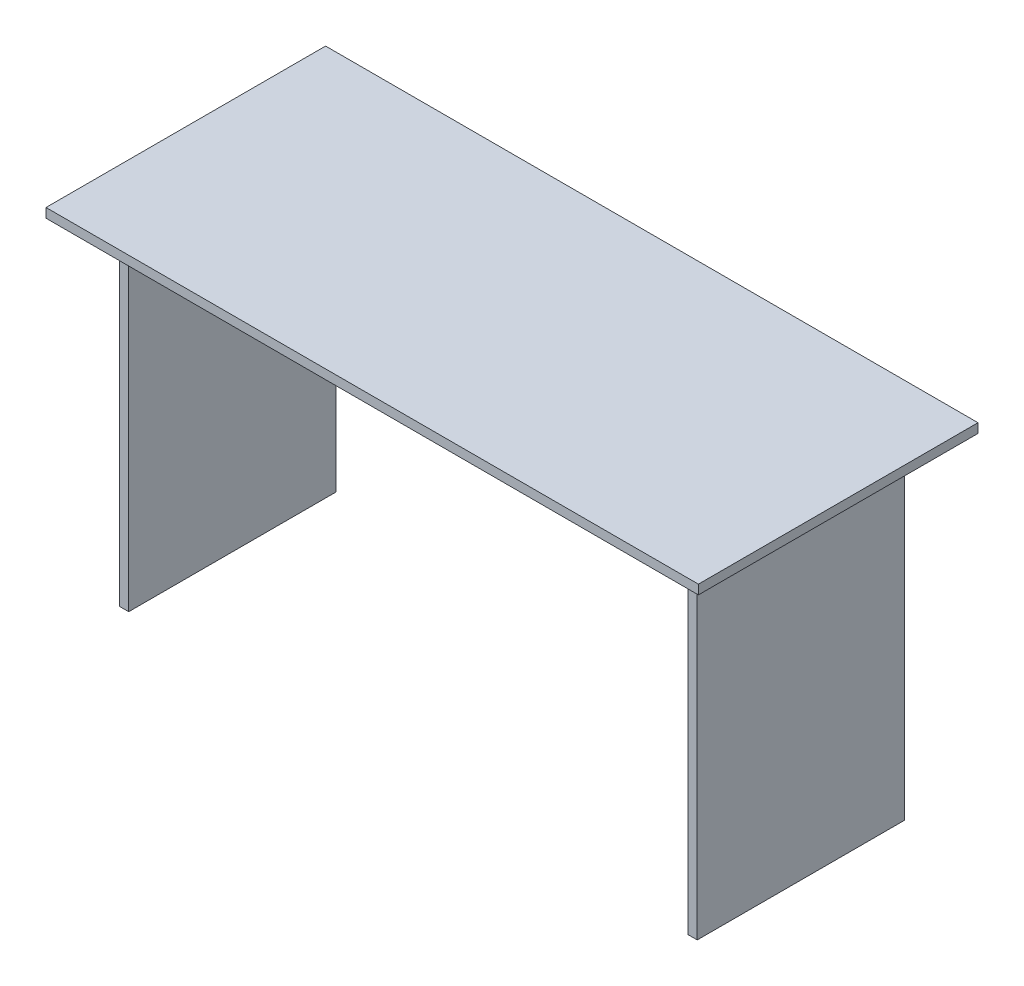
SolidWorks part; units mm, degrees
ref_plane "Front Plane" through (0, 0, 0) normal (0, 0, 1) x (1, 0, 0)
ref_plane "Top Plane" through (0, 0, 0) normal (0, 1, 0) x (1, 0, 0)
ref_plane "Right Plane" through (0, 0, 0) normal (1, 0, 0) x (0, 0, -1)
sketch "Sketch1" plane through (0, 0, 0) normal (0, 1, 0) x (1, 0, 0)
  line L1 (700, -300) -> (-700, -300)
  line L2 (700, -300) -> (700, 300)
  line L3 (700, 300) -> (-700, 300)
  line L4 (-700, -300) -> (-700, 300)
  line L5 (700, -300) -> (-700, 300) construction
  line L6 (700, 300) -> (-700, -300) construction
  point P0 (0, 0)
  dimension "D1" = 1400
  dimension "D2" = 600
extrude "Boss-Extrude1" add sketch "Sketch1" against normal blind 20
sketch "Sketch2" plane through (0, -20, 0) normal (0, -1, 0) x (1, 0, 0)
  line L0 (0, 300) -> (0, -300) construction
  line L1 (-700, 300) -> (700, 300) construction
  line L2 (700, -300) -> (-700, -300) construction
  line L3 (700, 300) -> (700, -300) construction
  line L4 (600, 222.5) -> (620, 222.5)
  line L5 (600, 222.5) -> (600, -222.5)
  line L6 (600, -222.5) -> (620, -222.5)
  line L7 (620, 222.5) -> (620, -222.5)
  line L8 (600, 222.5) -> (620, -222.5) construction
  line L9 (600, -222.5) -> (620, 222.5) construction
  line L10 (-600, -222.5) -> (-620, -222.5)
  line L11 (-620, 222.5) -> (-620, -222.5)
  line L12 (-600, 222.5) -> (-620, 222.5)
  line L13 (-600, 222.5) -> (-600, -222.5)
  point P6 (610, 0)
  point P11 (0, 0)
  dimension "D1" = 445
  dimension "D2" = 20
  dimension "D3" = 80
extrude "Boss-Extrude2" add sketch "Sketch2" along normal blind 720
sketch "Sketch3" plane through (0, -20, 0) normal (0, -1, 0) x (1, 0, 0)
  line L0 (-600, -222.5) -> (-600, 222.5) construction
  line L1 (600, -197.5) -> (-600, -197.5)
  line L2 (600, -197.5) -> (600, -177.5)
  line L3 (600, -177.5) -> (-600, -177.5)
  line L4 (-600, -197.5) -> (-600, -177.5)
  line L5 (600, -197.5) -> (-600, -177.5) construction
  line L6 (600, -177.5) -> (-600, -197.5) construction
  line L7 (600, -222.5) -> (620, -222.5) construction
  point P0 (0, -187.5)
  point P9 (0, 0)
  dimension "D1" = 20
  dimension "D2" = 25
extrude "Boss-Extrude3" add sketch "Sketch3" along normal blind 450
sketch "Sketch4" plane through (0, -20, 0) normal (0, -1, 0) x (1, 0, 0)
  line L0 (600, 222.5) -> (600, -177.5) construction
  line L1 (-600, -177.5) -> (600, -177.5)
  line L2 (-600, -177.5) -> (-600, -27.5)
  line L3 (-600, -27.5) -> (600, -27.5)
  line L4 (600, -177.5) -> (600, -27.5)
  line L5 (-600, 0) -> (600, 0) construction
  line L6 (-600, -177.5) -> (-600, 222.5) construction
  line L7 (600, 222.5) -> (600, -222.5) construction
  line L8 (-600, 27.5) -> (600, 27.5)
  line L9 (600, 177.5) -> (600, 27.5)
  line L10 (-600, 177.5) -> (600, 177.5)
  line L11 (-600, 177.5) -> (-600, 27.5)
  dimension "D1" = 150
extrude "Boss-Extrude4" add sketch "Sketch4" along normal blind 20
